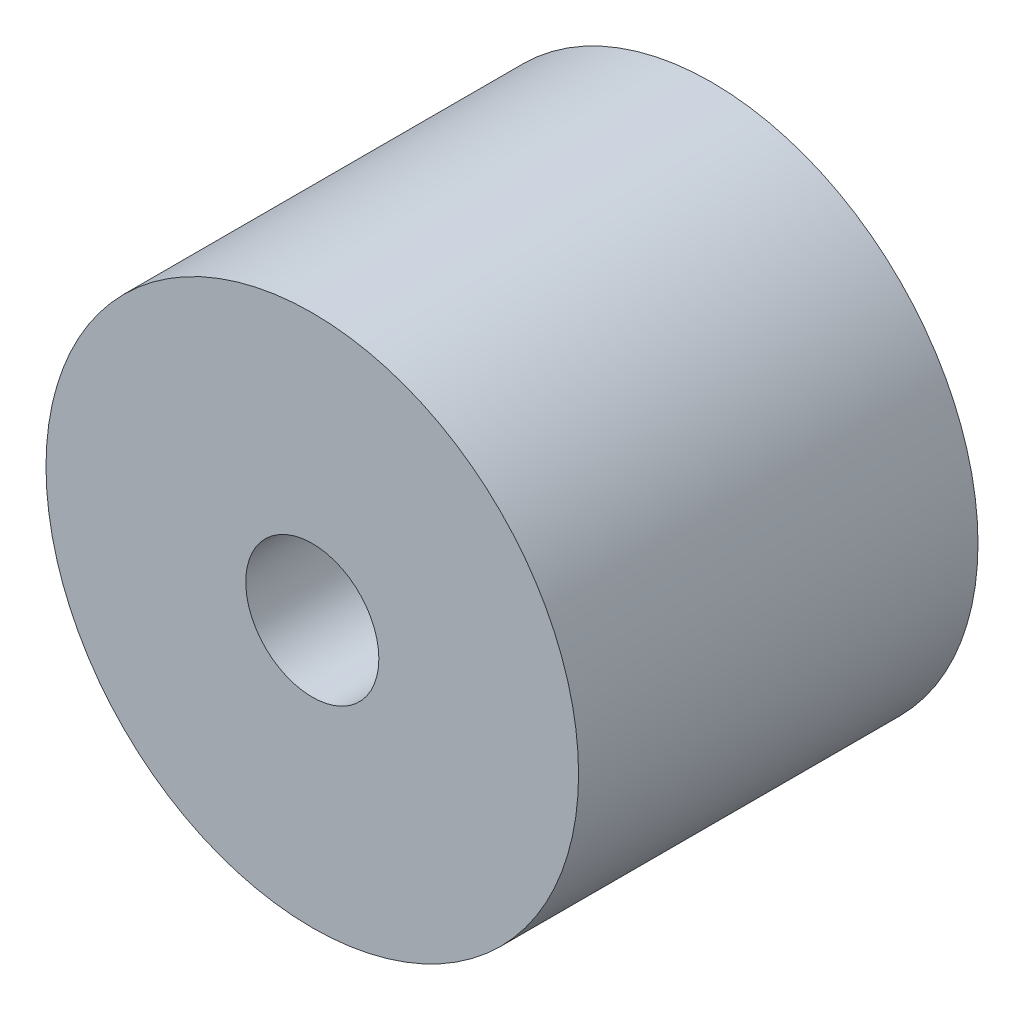
SolidWorks part; units mm, degrees
material "1023 Carbon Steel Sheet (SS)"
ref_plane "Front Plane" through (0, 0, 0) normal (0, 0, 1) x (1, 0, 0)
ref_plane "Top Plane" through (0, 0, 0) normal (0, 1, 0) x (1, 0, 0)
ref_plane "Right Plane" through (0, 0, 0) normal (1, 0, 0) x (0, 0, -1)
sketch "Sketch1" plane through (0, 0, 0) normal (0, 0, 1) x (1, 0, 0)
  circle A0 centre (0, 0) radius 3.175
  circle A1 centre (0, 0) radius 0.7937
  dimension "D1" = 1.5875
  dimension "D2" = 6.35
extrude "Boss-Extrude1" add sketch "Sketch1" along normal blind 4.7625
